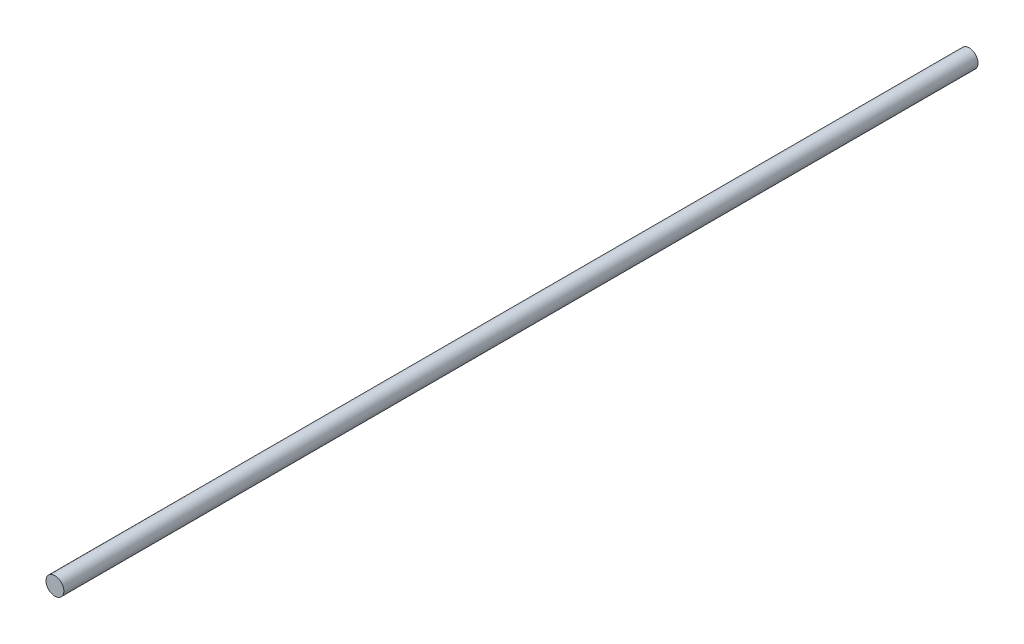
SolidWorks part; units mm, degrees
ref_plane "Alzado" through (0, 0, 0) normal (0, 0, 1) x (1, 0, 0)
ref_plane "Planta" through (0, 0, 0) normal (0, 1, 0) x (1, 0, 0)
ref_plane "Vista lateral" through (0, 0, 0) normal (1, 0, 0) x (0, 0, -1)
sketch "Croquis1" plane through (0, 0, 0) normal (0, 0, 1) x (1, 0, 0)
  circle A0 centre (0, 0) radius 4
  dimension "D1" = 8
extrude "Saliente-Extruir2" add sketch "Croquis1" along normal blind 410
